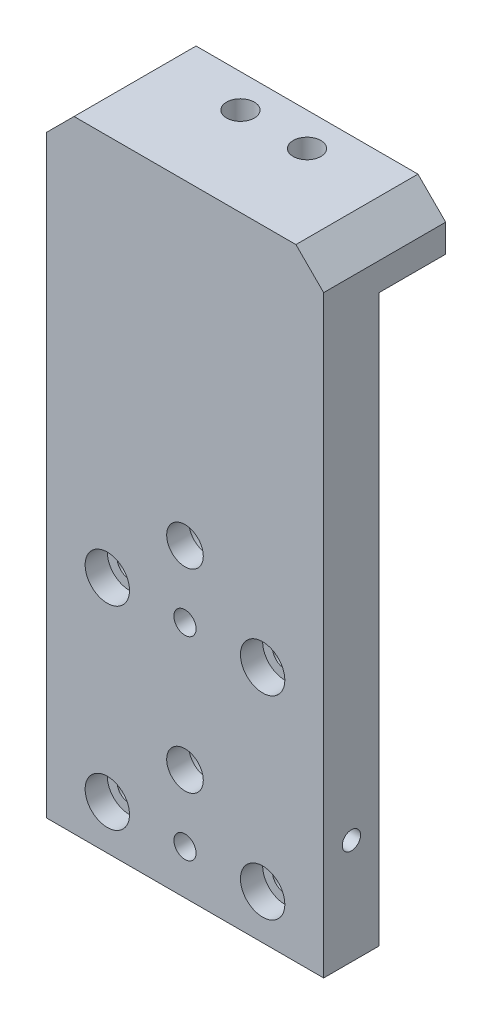
SolidWorks part; units mm, degrees
ref_plane "Front Plane" through (0, 0, 0) normal (0, 0, 1) x (1, 0, 0)
ref_plane "Top Plane" through (0, 0, 0) normal (0, 1, 0) x (1, 0, 0)
ref_plane "Right Plane" through (0, 0, 0) normal (1, 0, 0) x (0, 0, -1)
sketch "Sketch1" plane through (0, 0, 0) normal (0, 0, 1) x (1, 0, 0)
  line L1 (-20.6767, 24.1541) -> (29.3233, 24.1541)
  line L2 (-20.6767, 24.1541) -> (-20.6767, -87.8459)
  line L3 (-20.6767, -87.8459) -> (29.3233, -87.8459)
  line L4 (29.3233, 24.1541) -> (29.3233, -87.8459)
  circle A0 centre (4.3233, -67.8459) radius 3.3
  circle A1 centre (4.3233, -44.8459) radius 2
  circle A2 centre (4.3233, -32.8459) radius 3.3
  circle A3 centre (18.3233, -79.8459) radius 2.25
  circle A4 centre (-9.6767, -79.8459) radius 2.25
  circle A5 centre (-9.6767, -44.8459) radius 2.25
  circle A6 centre (18.3233, -44.8459) radius 2.25
  circle A7 centre (4.3233, -79.8459) radius 2
  point P18 (0, 0)
  dimension "D3" = 35
  dimension "D5" = 6.6
  dimension "D6" = 4.5
  dimension "D7" = 43
  dimension "D8" = 8
  dimension "D9" = 28
  dimension "D11" = 4
  dimension "D1" = 50
  dimension "D2" = 112
  dimension "D4" = 20
  dimension "D10" = 11
extrude "Boss-Extrude1" add sketch "Sketch1" along normal blind 10
sketch "Sketch2" plane through (0, 0, 0) normal (0, 0, -1) x (-1, 0, 0)
  circle A0 centre (-4.3233, -32.8459) radius 5.5
  circle A1 centre (-4.3233, -67.8459) radius 5.5
  dimension "D1" = 11
extrude "Cut-Extrude1" cut sketch "Sketch2" against normal blind 6
sketch "Sketch3" plane through (0, 0, 10) normal (0, 0, 1) x (1, 0, 0)
  circle A0 centre (-9.6767, -44.8459) radius 4
  circle A1 centre (18.3233, -44.8459) radius 4
  circle A2 centre (18.3233, -79.8459) radius 4
  circle A3 centre (-9.6767, -79.8459) radius 4
  dimension "D1" = 8
extrude "Cut-Extrude2" cut sketch "Sketch3" against normal blind 4
sketch "Sketch4" plane through (0, 0, 0) normal (0, 0, -1) x (-1, 0, 0)
  line L0 (20.6767, 24.1541) -> (20.6767, -87.8459) construction
  line L1 (-29.3233, 24.1541) -> (20.6767, 24.1541)
  line L2 (-29.3233, 24.1541) -> (-29.3233, 14.1541)
  line L3 (-29.3233, 14.1541) -> (20.6767, 14.1541)
  line L4 (20.6767, 24.1541) -> (20.6767, 14.1541)
  dimension "D1" = 10
extrude "Boss-Extrude2" add sketch "Sketch4" along normal blind 12
hole_wizard "M4 Tapped Hole1" positions "Sketch5" profile "Sketch6" tap size "M4" standard "ISO"
sketch "Sketch5" plane through (29.3233, 0, 0) normal (1, 0, 0) x (0, 0, -1)
  line L0 (-10, -87.8459) -> (-10, 24.1541) construction
  line L1 (-10, -87.8459) -> (0, -87.8459) construction
  point P0 (-5, -68.8459)
  dimension "D1" = 5
  dimension "D2" = 19
sketch "Sketch6" plane through (29.3233, -68.8459, 5) normal (0, 1, 0) x (0, 0, -1)
  line L0 (0, 0) -> (0, 8.9914)
  line L1 (0, 8.9914) -> (1.65, 8)
  line L2 (1.65, 8) -> (1.65, 0)
  line L5 (1.65, 0) -> (0, 0)
  line L10 (0, 8.9914) -> (-1.65, 8) construction
  line L11 (0, -6.35) -> (0, 107.95) construction
  dimension "Tap Drill Dia." = 3.3
  dimension "Tap Drill Depth" = 8
  dimension "Drill Angle" = 118
cosmetic thread "Hole Thread1" parameters "D1"=8, "D2"=4
hole_wizard "M4 Tapped Hole2" positions "Sketch7" profile "Sketch8" tap size "M4" standard "ISO"
sketch "Sketch7" plane through (-20.6767, 0, 0) normal (-1, 0, 0) x (0, 0, 1)
  line L0 (10, -87.8459) -> (0, -87.8459) construction
  line L1 (10, 24.1541) -> (10, -87.8459) construction
  point P0 (5, -68.8459)
  point P9 (4.2561, -69.4939)
  point P10 (0, 0)
  dimension "D1" = 19
  dimension "D2" = 5
sketch "Sketch8" plane through (-20.6767, -68.8459, 5) normal (0, 1, 0) x (0, 0, 1)
  line L0 (0, 0) -> (0, 8.9914)
  line L1 (0, 8.9914) -> (1.65, 8)
  line L2 (1.65, 8) -> (1.65, 0)
  line L5 (1.65, 0) -> (0, 0)
  line L10 (0, 8.9914) -> (-1.65, 8) construction
  line L11 (0, -6.35) -> (0, 107.95) construction
  dimension "Tap Drill Dia." = 3.3
  dimension "Tap Drill Depth" = 8
  dimension "Drill Angle" = 118
cosmetic thread "Hole Thread2" parameters "D1"=8, "D2"=4
chamfer "Chamfer1" distance 5 angle 45 2 edges at (-20.6767, 24.1541, -1) (29.3233, 24.1541, -1)
hole_wizard "M6 Tapped Hole1" positions "Sketch9" profile "Sketch10" tap size "M6" standard "ISO"
sketch "Sketch9" plane through (0, 24.1541, 0) normal (0, 1, 0) x (1, 0, 0)
  line L0 (24.3233, -10) -> (-15.6767, -10) construction
  line L1 (29.3233, 12) -> (29.3233, -10) construction
  point P0 (10.3233, 6)
  point P2 (-1.6767, 6)
  dimension "D1" = 12
  dimension "D2" = 16
  dimension "D3" = 19
sketch "Sketch10" plane through (10.3233, 24.1541, -6) normal (1, 0, 0) x (0, 0, 1)
  line L0 (0, 0) -> (0, 16.5022)
  line L1 (0, 16.5022) -> (2.5, 15)
  line L2 (2.5, 15) -> (2.5, 0)
  line L5 (2.5, 0) -> (0, 0)
  line L10 (0, 16.5022) -> (-2.5, 15) construction
  line L11 (0, -6.35) -> (0, 107.95) construction
  dimension "Tap Drill Dia." = 5
  dimension "Tap Drill Depth" = 15
  dimension "Drill Angle" = 118
cosmetic thread "Hole Thread3" parameters "D1"=10, "D2"=6
cosmetic thread "Hole Thread4" parameters "D1"=10, "D2"=6
